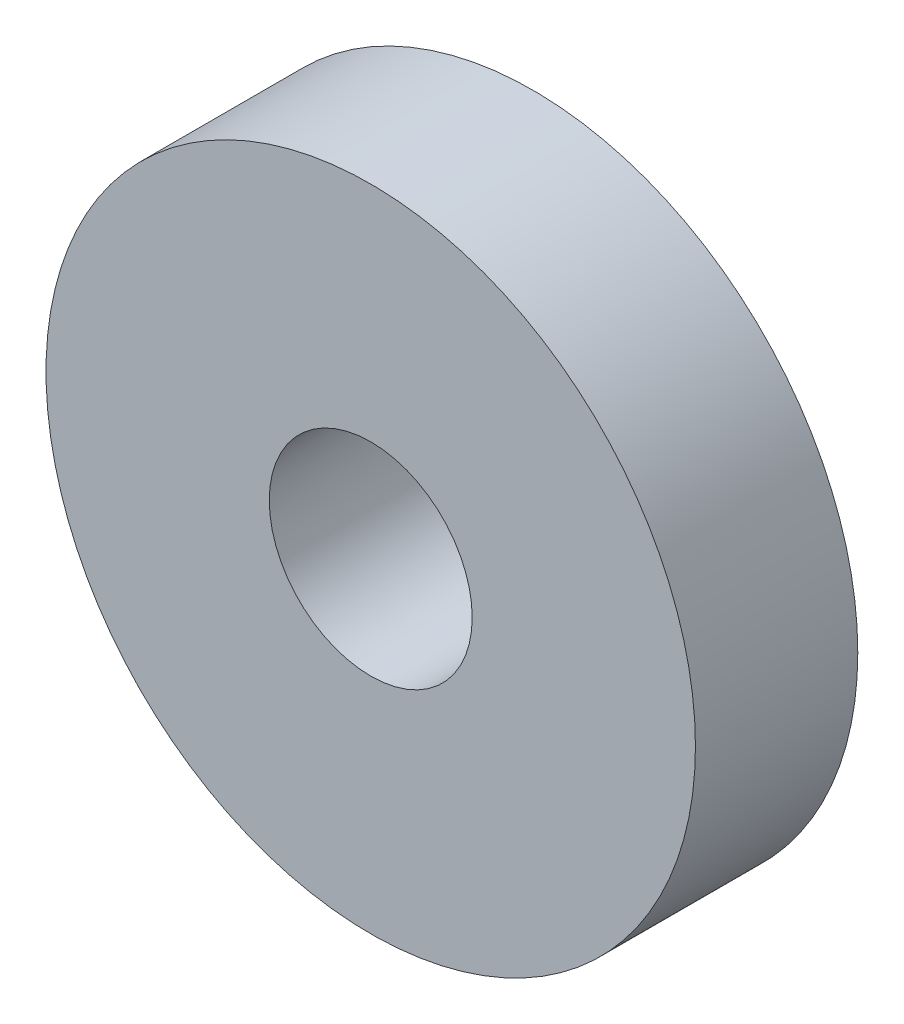
SolidWorks part; units mm, degrees
ref_plane "Plane1" through (0, 0, 0) normal (0, 0, 1) x (1, 0, 0)
ref_plane "Plane2" through (0, 0, 0) normal (0, 1, 0) x (1, 0, 0)
ref_plane "Plane3" through (0, 0, 0) normal (1, 0, 0) x (0, 0, -1)
sketch "Esquisse1" plane through (0, 0, 0) normal (0, 0, 1) x (1, 0, 0)
  circle A0 centre (0, 0) radius 4
  circle A1 centre (0, 0) radius 1.25
  dimension "D1" = 2.5
  dimension "D2" = 8
extrude "Base-Extrusion" add sketch "Esquisse1" along normal blind 2
